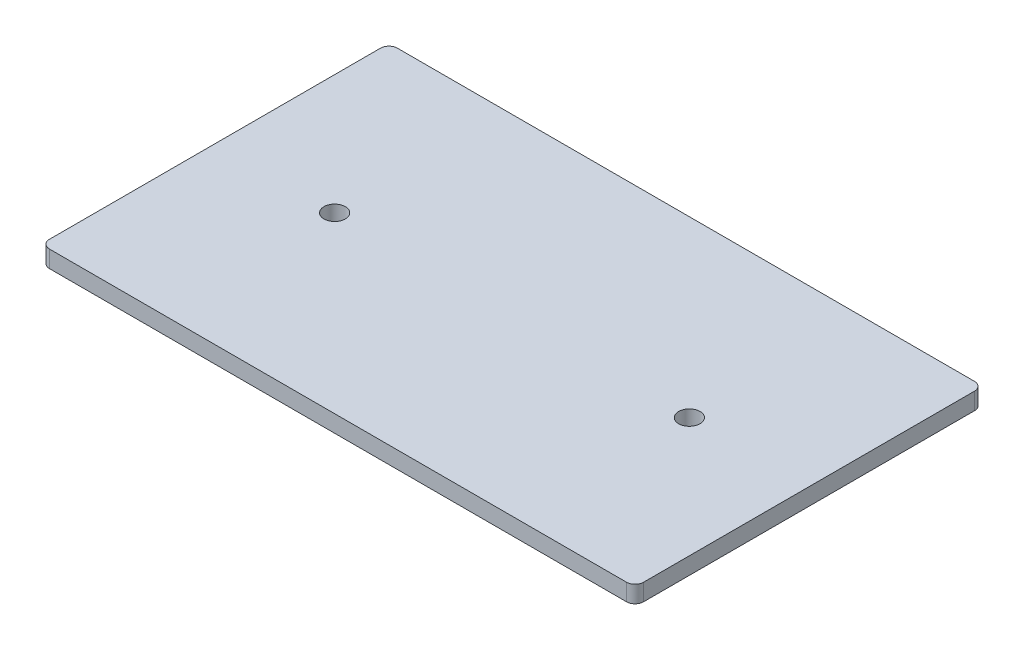
SolidWorks part; units mm, degrees
ref_plane "Front Plane" through (0, 0, 0) normal (0, 0, 1) x (1, 0, 0)
ref_plane "Top Plane" through (0, 0, 0) normal (0, 1, 0) x (1, 0, 0)
ref_plane "Right Plane" through (0, 0, 0) normal (1, 0, 0) x (0, 0, -1)
sketch "Sketch1" plane through (0, 0, 0) normal (0, 1, 0) x (1, 0, 0)
  line L1 (44.45, -26.035) -> (-44.45, -26.035)
  line L2 (44.45, -26.035) -> (44.45, 26.035)
  line L3 (44.45, 26.035) -> (-44.45, 26.035)
  line L4 (-44.45, -26.035) -> (-44.45, 26.035)
  line L5 (44.45, -26.035) -> (-44.45, 26.035) construction
  line L6 (44.45, 26.035) -> (-44.45, -26.035) construction
  point P0 (0, 0)
  dimension "D1" = 88.9
  dimension "D2" = 52.07
extrude "Boss-Extrude1" add sketch "Sketch1" along normal blind 2.54
fillet "Fillet1" radius 1.27 4 edges at (-44.45, 1.27, -26.035) (44.45, 1.27, -26.035) (-44.45, 1.27, 26.035) (44.45, 1.27, 26.035)
sketch "Sketch2" plane through (0, 2.54, 0) normal (0, 1, 0) x (1, 0, 0)
  line L0 (-26.543, 0) -> (26.543, 0) construction
  circle A0 centre (-26.543, 0) radius 1.6
  circle A1 centre (26.543, 0) radius 1.6
  dimension "D2" = 3.2
  dimension "D1" = 53.086
extrude "Cut-Extrude1" cut sketch "Sketch2" against normal blind 7.62
